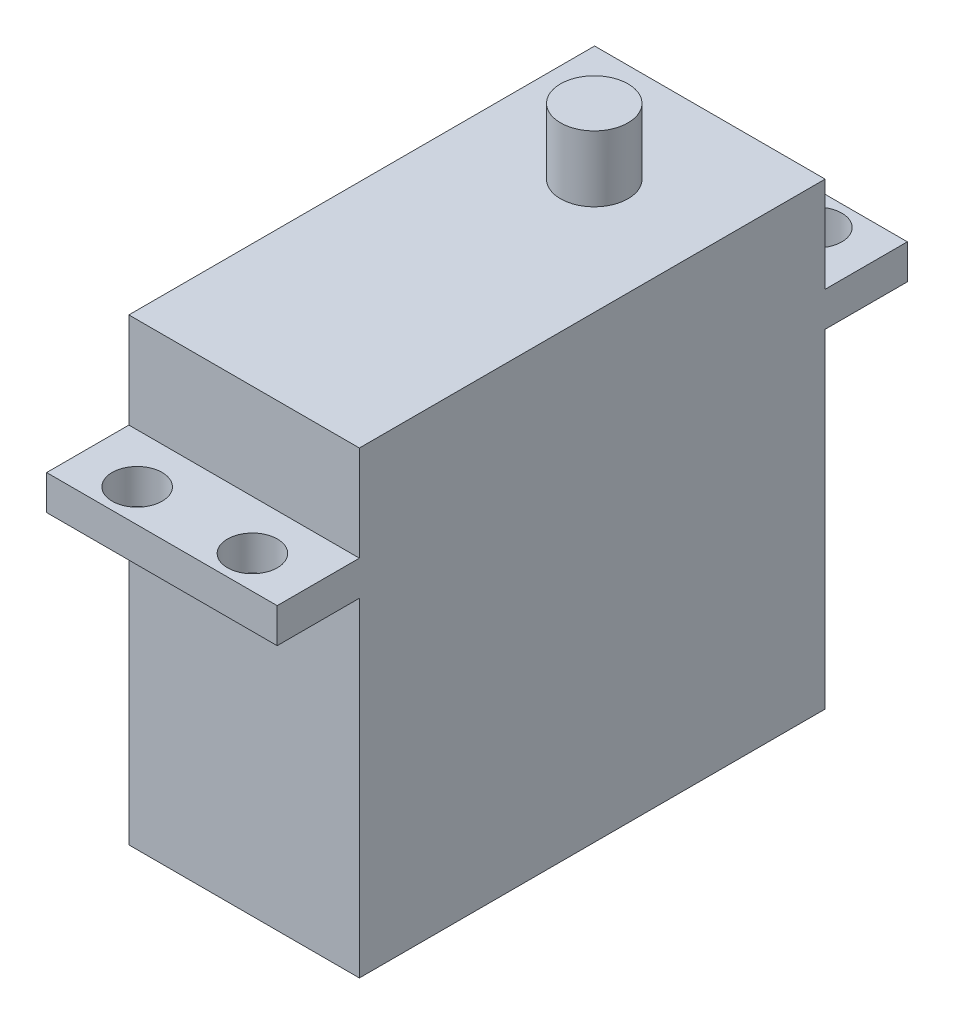
SolidWorks part; units mm, degrees
material "ABS"
ref_plane "Front Plane" through (0, 0, 0) normal (0, 0, 1) x (1, 0, 0)
ref_plane "Top Plane" through (0, 0, 0) normal (0, 1, 0) x (1, 0, 0)
ref_plane "Right Plane" through (0, 0, 0) normal (1, 0, 0) x (0, 0, -1)
sketch "Sketch4" plane through (0, 0, 0) normal (0, 1, 0) x (1, 0, 0)
  circle A0 centre (0, 0) radius 10
  dimension "D1" = 20
sketch "Sketch1" plane through (0, 0, 0) normal (0, 1, 0) x (1, 0, 0)
  line L1 (-9.9695, -30.2844) -> (9.9695, -30.2844)
  line L2 (-9.9695, -30.2844) -> (-9.9695, 10)
  line L3 (-9.9695, 10) -> (9.9695, 10)
  line L4 (9.9695, -30.2844) -> (9.9695, 10)
  line L5 (-9.9695, -30.2844) -> (9.9695, 10) construction
  line L6 (-9.9695, 10) -> (9.9695, -30.2844) construction
  circle A1 centre (0, 0) radius 10 construction
  point P4 (0, -10.1422)
  dimension "D1" = 19.939
  dimension "D2" = 40.2844
extrude "Body" add sketch "Sketch1" along normal blind 39.7002
sketch "Sketch2" plane through (0, 39.7002, 0) normal (0, 1, 0) x (1, 0, 0)
  line L0 (0, 10) -> (0, -30.2844) construction
  line L1 (9.9695, 10) -> (-9.9695, 10) construction
  line L2 (-9.9695, -30.2844) -> (9.9695, -30.2844) construction
  circle A0 centre (0, 0) radius 2.921
  dimension "D2" = 5.842
extrude "Axle" add sketch "Sketch2" along normal blind 5.6896
sketch "Sketch3" plane through (0, 0, 0) normal (0, 1, 0) x (1, 0, 0)
  line L0 (9.9695, -30.2844) -> (9.9695, 10) construction
  line L1 (-9.9695, 10) -> (9.9695, 10)
  line L2 (-9.9695, 10) -> (-9.9695, 17.112)
  line L3 (-9.9695, 17.112) -> (9.9695, 17.112)
  line L4 (9.9695, 10) -> (9.9695, 17.112)
  line L5 (-9.9695, 10) -> (9.9695, 17.112) construction
  line L6 (-9.9695, 17.112) -> (9.9695, 10) construction
  line L7 (-9.9695, 12.1082) -> (9.9695, 12.1082) construction
  line L8 (-9.9695, -30.2844) -> (10, -30.2844) construction
  line L9 (-9.9695, -30.2844) -> (-9.9695, -37.3964) construction
  line L10 (-9.9695, -37.3964) -> (10, -37.3964) construction
  line L11 (10, -30.2844) -> (10, -37.3964) construction
  line L12 (-9.9695, -30.2844) -> (10, -37.3964) construction
  line L13 (-9.9695, -37.3964) -> (10, -30.2844) construction
  line L14 (0, 13.556) -> (0, 21.3026) construction
  circle A0 centre (-4.9848, 14.2672) radius 2.159
  circle A1 centre (4.9848, 14.2672) radius 2.159
  point P4 (0, 13.556)
  point P12 (0.0153, -33.8404)
  dimension "D2" = 4.318
  dimension "D1" = 7.112
  dimension "D3" = 9.9695
  dimension "D5" = 2.1082
extrude "Wings" add sketch "Sketch3" along normal blind 3 from offset 28.448 contours A1 L3 A0 L2 L1 L4
ref_plane "Plane1" through (0, 0, 10.1422) normal (0, 0, 1) x (1, 0, 0)
mirror "Mirror1" about plane through (0, 0, 10.1422) normal (0, 0, 1) of "Wings"
